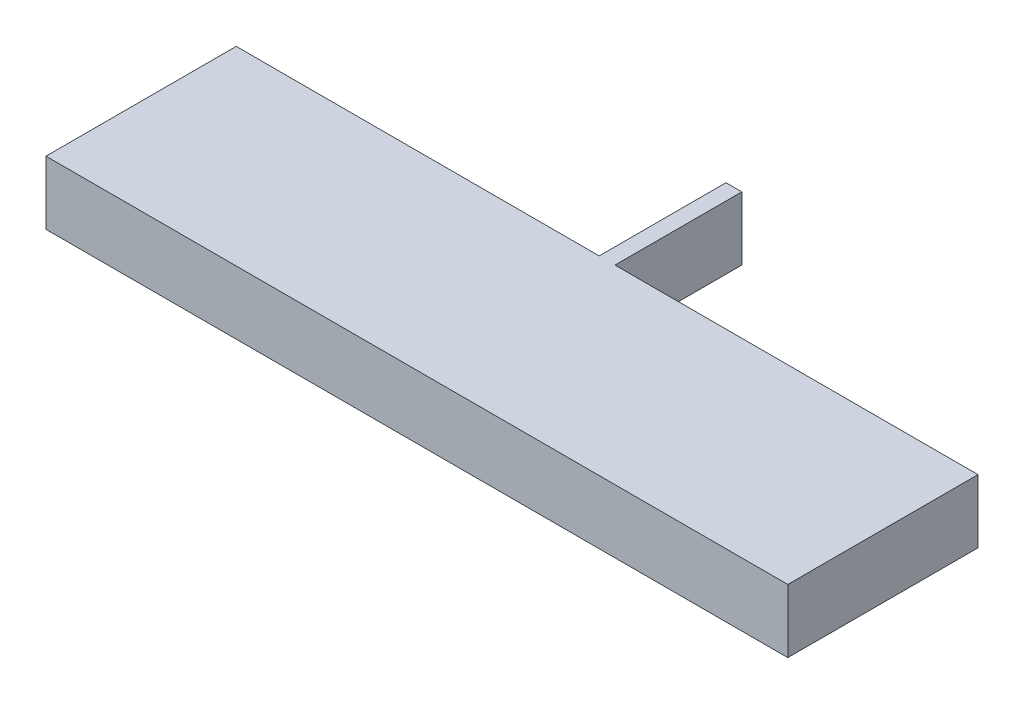
SolidWorks part; units mm, degrees
ref_plane "Front Plane" through (0, 0, 0) normal (0, 0, 1) x (1, 0, 0)
ref_plane "Top Plane" through (0, 0, 0) normal (0, 1, 0) x (1, 0, 0)
ref_plane "Right Plane" through (0, 0, 0) normal (1, 0, 0) x (0, 0, -1)
sketch "Sketch1" plane through (0, 0, 0) normal (0, 1, 0) x (1, 0, 0)
  line L0 (0, 0) -> (0, -50000) construction
  line L1 (0, 0) -> (50000, 0) construction
  line L2 (-11.7, 3) -> (-0.25, 3)
  line L3 (-11.7, 3) -> (-11.7, -3)
  line L4 (-11.7, -3) -> (11.7, -3)
  line L5 (11.7, 3) -> (11.7, -3)
  line L6 (-0.25, 7) -> (-0.25, 3)
  line L7 (0.25, 7) -> (0.25, 3)
  line L8 (0.25, 3) -> (11.7, 3)
  line L9 (-0.25, 7) -> (0.25, 7)
  dimension "D12" = 0.5
  dimension "D13" = 11.45
  dimension "D14" = 23.4
  dimension "D15" = 11.45
  dimension "D16" = 6
  dimension "D17" = 4
extrude "Boss-Extrude1" add sketch "Sketch1" along normal blind 2
sketch "Sketch2" plane through (0, 0, 0) normal (0, -1, 0) x (1, 0, 0)
  point P0 (0, 0)
sketch "Orientation Sketch" plane through (0, 0, 0) normal (0, -1, 0) x (-1, 0, 0)
  line L0 (11.7, 3) -> (11.7, -3) construction
  line L1 (0.25, 3) -> (11.7, 3) construction
  line L2 (0.25, 7) -> (0.25, 3) construction
  line L3 (-0.25, 7) -> (0.25, 7) construction
  line L4 (-0.25, 3) -> (-0.25, 7) construction
  line L5 (-11.7, 3) -> (-0.25, 3) construction
  line L6 (-11.7, -3) -> (-11.7, 3) construction
  line L7 (11.7, -3) -> (-11.7, -3) construction
  line L8 (11.7, 3) -> (11.7, -3)
  line L9 (0.25, 3) -> (11.7, 3)
  line L10 (0.25, 7) -> (0.25, 3)
  line L11 (-0.25, 7) -> (0.25, 7)
  line L12 (-0.25, 3) -> (-0.25, 7)
  line L13 (-11.7, 3) -> (-0.25, 3)
  line L14 (-11.7, -3) -> (-11.7, 3)
  line L15 (11.7, -3) -> (-11.7, -3)
  point P3 (0, 2)
other "FormTool1"
